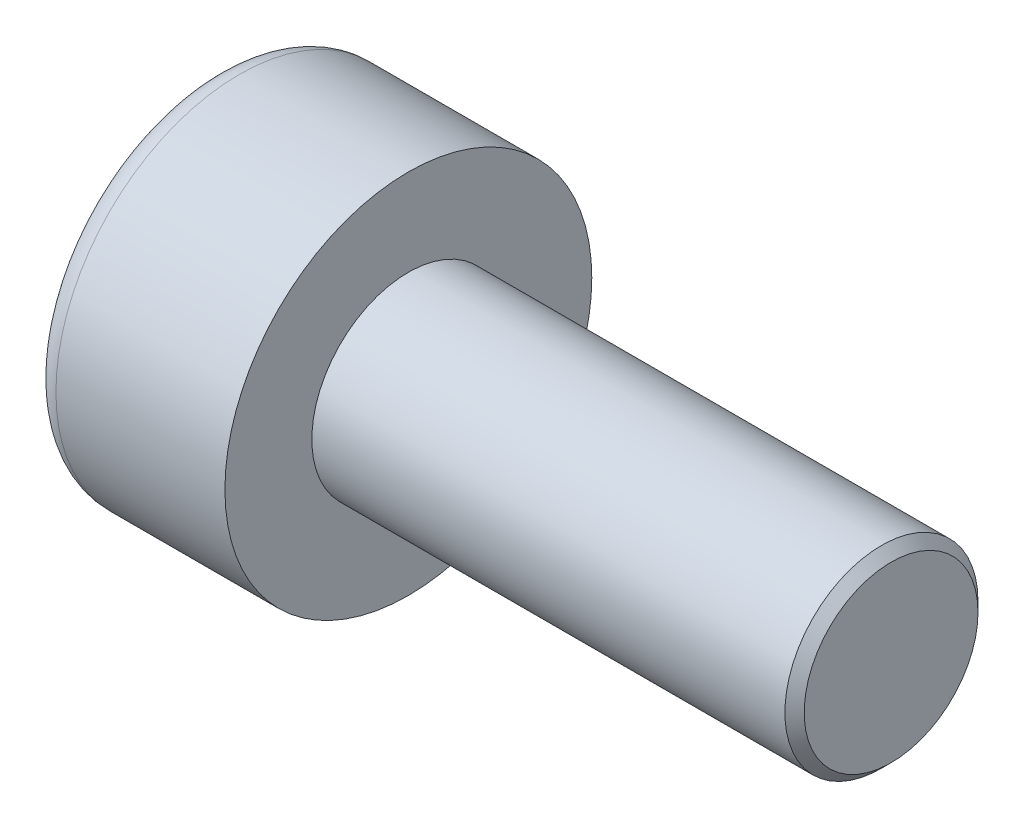
SolidWorks part; units mm, degrees
ref_plane "Front" through (0, 0, 0) normal (0, 0, 1) x (1, 0, 0)
ref_plane "Top" through (0, 0, 0) normal (0, 1, 0) x (1, 0, 0)
ref_plane "Right" through (0, 0, 0) normal (1, 0, 0) x (0, 0, -1)
sketch "Sketch1" plane through (0, 0, 0) normal (1, 0, 0) x (0, 0, -1)
  circle A0 centre (0, 0) radius 1.9
  dimension "dk" = 3.8
extrude "BaseHead" add sketch "Sketch1" along normal blind 2
sketch "Sketch2" plane through (2, 0, 0) normal (1, 0, 0) x (0, 0, -1)
  circle A0 centre (0, 0) radius 1
  dimension "d" = 2
extrude "BaseBody" add sketch "Sketch2" along normal blind 5
cosmetic thread "ThreadCosmetic1" parameters "b"=10, "D2"=1.567
sketch "Sketch3" plane through (0, 0, 0) normal (1, 0, 0) x (0, 0, -1)
  line L1 (0.866, 0) -> (0.433, 0.75)
  line L2 (0.433, 0.75) -> (-0.433, 0.75)
  line L3 (-0.433, 0.75) -> (-0.866, 0)
  line L4 (-0.866, 0) -> (-0.433, -0.75)
  line L5 (-0.433, -0.75) -> (0.433, -0.75)
  line L6 (0.433, -0.75) -> (0.866, 0)
  circle A0 centre (0, 0) radius 0.75 construction
  dimension "s" = 1.5
  dimension "e" = 1.7321
extrude "HexagonSocket" cut sketch "Sketch3" along normal blind 1
sketch "Sketch4" plane through (-4.1961, 0.75, 0) normal (0, 0, 1) x (-1, 0, 0)
  line L0 (-5.1961, 1.5) -> (-5.6292, 0.75)
  line L2 (-5.6292, 0.75) -> (-5.1961, 0.75)
  line L3 (-5.1961, 0.75) -> (-5.1961, 1.5)
  line L4 (-5.0351, 0.75) -> (0.839, 0.75) construction
  line L5 (-11.1961, 0.75) -> (-6.1961, 0.75) construction
  line L6 (-6.1961, 0.75) -> (-4.1961, 0.75) construction
  dimension "m" = 60
revolve "Cut-Revolve1" cut sketch "Sketch4" angle 360 about L4
fillet "HeadFillet" [suppressed] radius 0.1
fillet "TopFillet" radius 0.25 1 edges at (0, 0, -1.9)
chamfer "Chamfer1" distance 0.1 angle 45 1 edges at (7, 0, -1)
sketch "Sketch5" plane through (0, 0, 0) normal (0, 0, 1) x (1, 0, 0)
  line L0 (6.9, 0.8125) -> (7.0083, 1)
  line L1 (7.0083, 1) -> (7.0083, 1.2165)
  line L2 (7.0083, 1.2165) -> (6.7918, 1.2165)
  line L3 (6.7918, 1.2165) -> (6.7918, 1)
  line L4 (6.7918, 1) -> (6.9, 0.8125)
  line L5 (0, 0) -> (7.8886, 0) construction
  line L6 (6.9, -1) -> (6.9, 1) construction
  dimension "D1" = 2
  dimension "D2" = 0.2165
revolve "Cut-Revolve10" [suppressed] cut sketch "Sketch5" angle 360 about L5
pattern_linear "LPattern10" [suppressed] count 38 spacing 0.2598 along (1, 0, 0)
equation "\"r1@TopFillet\" = \"d@Sketch2\" / 8"
equation "\"D1@Chamfer1\" = \"r@HeadFillet\""
equation "\"D1@Sketch5\" = \"d@Sketch2\""
equation "\"D2@Sketch5\" =  ( \"d@Sketch2\" - \"D2@ThreadCosmetic1\" )  / 2"
equation "\"D3@LPattern10\" = \"D2@Sketch5\" * 1.2"
equation "\"D1@LPattern10\" = \"b@ThreadCosmetic1\" / \"D3@LPattern10\""
